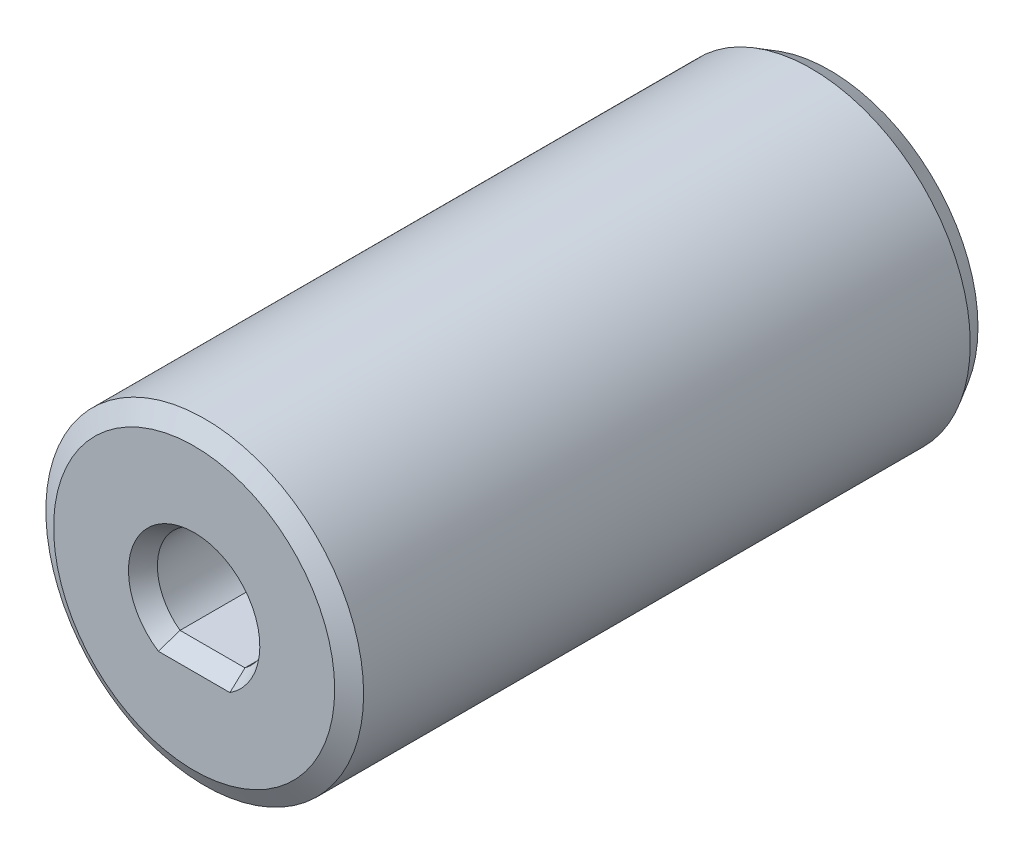
SolidWorks part; units mm, degrees
ref_plane "Top Plane" through (0, 0, 0) normal (0, 0, 1) x (1, 0, 0)
ref_plane "Front Plane" through (0, 0, 0) normal (0, 1, 0) x (1, 0, 0)
ref_plane "Right Plane" through (0, 0, 0) normal (1, 0, 0) x (0, 0, -1)
sketch "OD Profile Sketch" plane through (0, 0, 0) normal (0, 0, 1) x (1, 0, 0)
  circle A0 centre (0, 0) radius 7.5
  dimension "D1" = 15
extrude "OD Boss-Extrude" add sketch "OD Profile Sketch" along normal blind 30
sketch "Wheel Shaft Profile Sketch" plane through (0, 0, 0) normal (0, 0, 1) x (1, 0, 0)
  line L0 (1.9672, -1.7) -> (-1.9672, -1.7)
  line L1 (1.9672, 1.7) -> (-1.9672, 1.7)
  line L2 (0, -1.7) -> (0, 1.7) construction
  arc A0 (1.9672, -1.7) -> (1.9672, 1.7) centre (0, 0) ccw
  arc A1 (-1.9672, 1.7) -> (-1.9672, -1.7) centre (0, 0) ccw
  circle A2 centre (0, 0) radius 4.95
  point P9 (0, 0)
  dimension "D1" = 5.2
  dimension "D3" = 9.9
  dimension "D2" = 3.4
extrude "Wheel Shaft Cut-Extrude" cut sketch "Wheel Shaft Profile Sketch" along normal blind 10
sketch "NEMA17 Shaft Profile Sketch" plane through (0, 0, 30) normal (0, 0, 1) x (1, 0, 0)
  line L0 (-1.533, -2.1) -> (1.533, -2.1)
  arc A0 (1.533, -2.1) -> (-1.533, -2.1) centre (0, 0) ccw
  dimension "D1" = 4.7
  dimension "D2" = 5.2
extrude "NEMA17 Shaft Cut-Extrude" cut sketch "NEMA17 Shaft Profile Sketch" against normal blind 10
ref_plane "Tangent Plane" through (0, -7.5, 0) normal (0, -1, 0) x (-1, 0, 0)
hole_wizard "Tap Drill for M3x0.5" positions "Tap Drill for M3x0.5 Location Sketch" profile "Tap Drill for M3x0.5 Profile Sketch" hole size "M3x0.5" standard "ANSI Metric" end condition up to next
sketch "Tap Drill for M3x0.5 Location Sketch" plane through (0, -7.5, 0) normal (0, -1, 0) x (-1, 0, 0)
  line L1 (0, -5) -> (0, 0) construction
  line L3 (0, -5) -> (0, -25) construction
  point P0 (0, -25)
  point P2 (0, -5)
  dimension "D1" = 5
  dimension "D2" = 20
sketch "Tap Drill for M3x0.5 Profile Sketch" plane through (0, -7.5, 25) normal (1, 0, 0) x (0, 0, -1)
  line L0 (0, 0) -> (0, 5.4)
  line L1 (0, 5.4) -> (1.2, 5.4)
  line L2 (1.2, 5.4) -> (1.2, 0)
  line L5 (1.2, 0) -> (0, 0)
  line L11 (0, -6.35) -> (0, 107.95) construction
  dimension "Thru Hole Dia." = 2.4
  dimension "Thru Hole Depth" = 5.4
chamfer "Edge Chamfer (1mm x 60)" distance 0.5 angle 60 9 edges at (-2.6, 0, 0) (0, -1.7, 0) (2.6, 0, 0) (0, 1.7, 0) (4.95, 0, 0) (0, -2.1, 30) (0, 2.6, 30) (7.5, 0, 30) (7.5, 0, 0)
